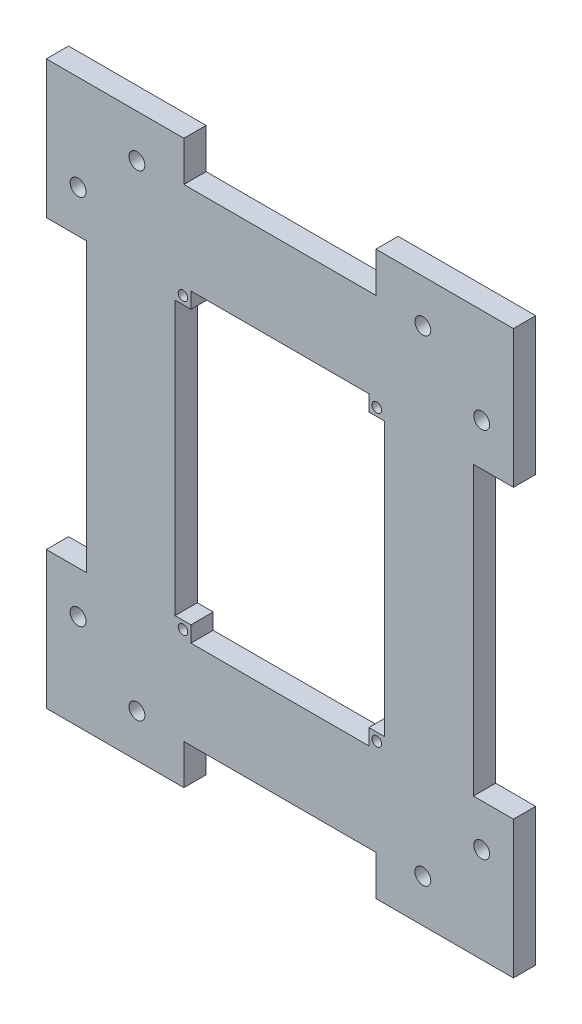
SolidWorks part; units mm, degrees
ref_plane "Front Plane" through (0, 0, 0) normal (0, 0, 1) x (1, 0, 0)
ref_plane "Top Plane" through (0, 0, 0) normal (0, 1, 0) x (1, 0, 0)
ref_plane "Right Plane" through (0, 0, 0) normal (1, 0, 0) x (0, 0, -1)
sketch "Sketch1" plane through (0, 0, 0) normal (0, 0, 1) x (1, 0, 0)
  line L1 (-28, 48) -> (28, 48)
  line L2 (-33, 43) -> (-33, -43)
  line L3 (-28, -48) -> (28, -48)
  line L4 (33, 43) -> (33, -43)
  line L11 (-33, 43) -> (-28, 43)
  line L12 (-28, 48) -> (-28, 43)
  line L17 (-30.2242, 75.9132) -> (30.2242, 75.9132)
  line L21 (60.9132, 45.2242) -> (60.9132, -45.2242)
  line L23 (55, 0) -> (-55, 0) construction
  line L24 (-33, -43) -> (-28, -43)
  line L25 (-28, -48) -> (-28, -43)
  line L30 (0, -55) -> (0, 55) construction
  line L35 (28, 48) -> (28, 43)
  line L36 (33, 43) -> (28, 43)
  line L37 (28, -48) -> (28, -43)
  line L38 (33, -43) -> (28, -43)
  line L44 (-30.2242, -75.9132) -> (30.2242, -75.9132)
  line L47 (-60.9132, 45.2242) -> (-60.9132, -45.2242)
  line L50 (-55.9132, 75.9132) -> (55.9132, 75.9132) construction
  line L51 (-60.9132, 45.2242) -> (-73.5198, 45.2242)
  line L52 (-30.2242, 75.9132) -> (-30.2242, 88.5198)
  line L53 (-30.2242, 88.5198) -> (-73.5198, 88.5198)
  line L54 (-73.5198, 45.2242) -> (-73.5198, 88.5198)
  line L55 (-30.2242, -75.9132) -> (-30.2242, -88.5198)
  line L56 (-30.2242, -88.5198) -> (-73.5198, -88.5198)
  line L57 (-55.9132, 75.9132) -> (-55.9132, 70.9132) construction
  line L58 (-60.9132, 70.9132) -> (-55.9132, 70.9132) construction
  line L59 (-60.9132, 70.9132) -> (-60.9132, -70.9132) construction
  line L60 (-60.9132, -45.2242) -> (-73.5198, -45.2242)
  line L61 (-73.5198, -45.2242) -> (-73.5198, -88.5198)
  line L62 (30.2242, -75.9132) -> (30.2242, -88.5198)
  line L63 (30.2242, -88.5198) -> (73.5198, -88.5198)
  line L64 (73.5198, -45.2242) -> (73.5198, -88.5198)
  line L65 (60.9132, -45.2242) -> (73.5198, -45.2242)
  line L66 (60.9132, 45.2242) -> (73.5198, 45.2242)
  line L67 (73.5198, 45.2242) -> (73.5198, 88.5198)
  line L68 (30.2242, 88.5198) -> (73.5198, 88.5198)
  line L69 (30.2242, 75.9132) -> (30.2242, 88.5198)
  line L70 (-55.9132, -75.9132) -> (55.9132, -75.9132) construction
  line L71 (-55.9132, -75.9132) -> (-55.9132, -70.9132) construction
  line L72 (-60.9132, -70.9132) -> (-55.9132, -70.9132) construction
  line L73 (55.9132, -75.9132) -> (55.9132, -70.9132) construction
  line L74 (60.9132, -70.9132) -> (55.9132, -70.9132) construction
  line L75 (60.9132, 70.9132) -> (60.9132, -70.9132) construction
  line L76 (60.9132, 70.9132) -> (55.9132, 70.9132) construction
  line L77 (55.9132, 75.9132) -> (55.9132, 70.9132) construction
  point P0 (0, 0)
  dimension "D2" = 5
  dimension "D3" = 66
  dimension "D4" = 96
  dimension "D5" = 5
extrude "Boss-Extrude1" add sketch "Sketch1" along normal blind 7
sketch "Sketch2" plane through (0, 0, 7) normal (0, 0, 1) x (1, 0, 0)
  circle A0 centre (30.5, -45.5) radius 1.5
  dimension "D1" = 3
extrude "Cut-Extrude1" cut sketch "Sketch2" against normal blind 10
mirror "Mirror1" about plane through (0, 0, 0) normal (1, 0, 0) of "Cut-Extrude1"
mirror "Mirror2" about plane through (0, 0, 0) normal (0, 1, 0) of "Cut-Extrude1", "Mirror1"
ref_plane "Plane1" through (0, 0, 3.5) normal (0, 0, -1) x (-1, 0, 0)
sketch "Sketch5" plane through (0, 0, 7) normal (0, 0, 1) x (1, 0, 0)
  circle A0 centre (-45, 75) radius 2.5 construction
  circle A1 centre (-45, 75) radius 2.5
extrude "Cut-Extrude4" cut sketch "Sketch5" against normal through all both and the other way through all
mirror "Mirror5" about plane through (0, 0, 0) normal (0, 1, 0) of "Cut-Extrude4"
mirror "Mirror6" about plane through (0, 0, 0) normal (1, 0, 0) of "Cut-Extrude4", "Mirror5"
sketch "Sketch6" plane through (0, 0, 0) normal (0, 0, -1) x (-1, 0, 0)
  circle A0 centre (63.5198, 58.5198) radius 2.5 construction
  circle A1 centre (63.5198, 58.5198) radius 2.5
extrude "Cut-Extrude5" cut sketch "Sketch6" against normal through all both and the other way through all
ref_plane "Plane2" through (0, 0, 0) normal (1, 0, 0) x (0, 0, -1)
mirror "Mirror8" about plane through (0, 0, 0) normal (1, 0, 0) of "Cut-Extrude5"
mirror "Mirror9" about plane through (0, 0, 0) normal (0, 1, 0) of "Cut-Extrude5", "Mirror8"
